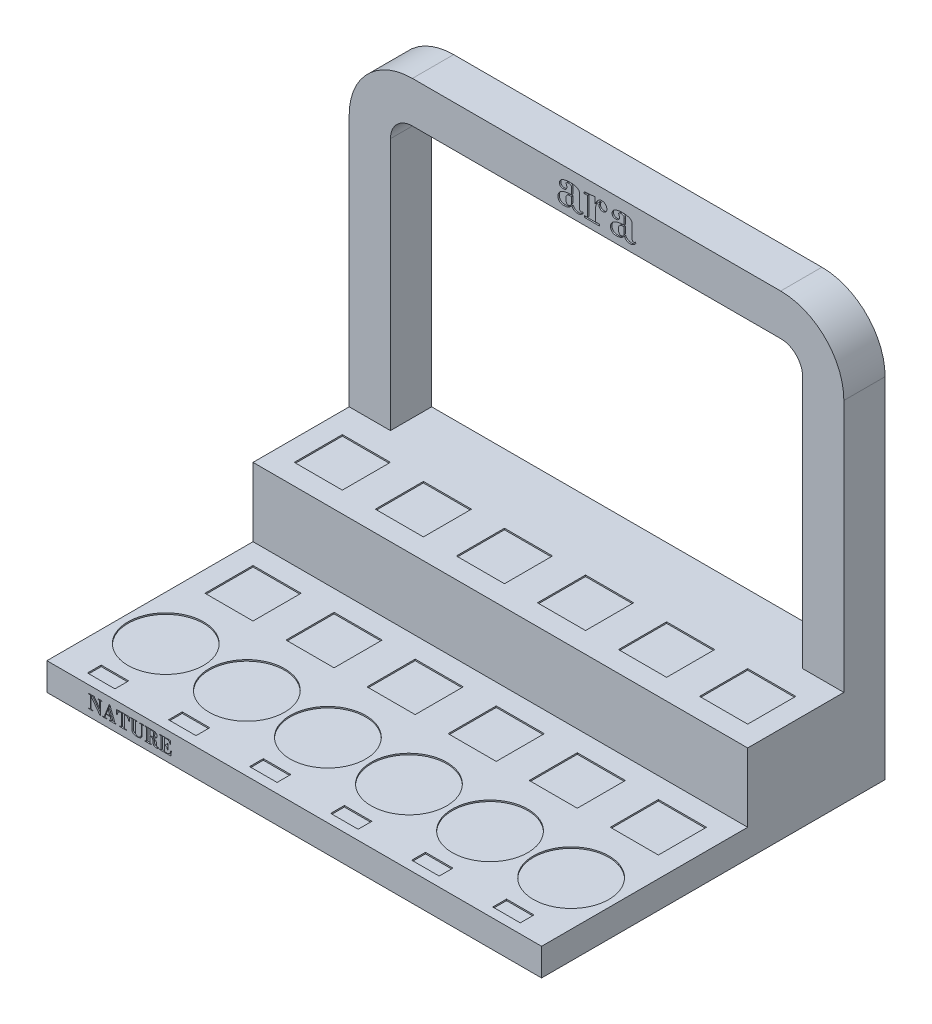
SolidWorks part; units mm, degrees
ref_plane "Front Plane" through (0, 0, 0) normal (0, 0, 1) x (1, 0, 0)
ref_plane "Top Plane" through (0, 0, 0) normal (0, 1, 0) x (1, 0, 0)
ref_plane "Right Plane" through (0, 0, 0) normal (1, 0, 0) x (0, 0, -1)
sketch "Sketch1" plane through (0, 0, 0) normal (1, 0, 0) x (0, 0, -1)
  line L0 (0, 0) -> (150, 0)
  line L1 (150, 0) -> (150, 50)
  line L2 (150, 50) -> (250, 50)
  line L3 (250, 50) -> (250, -20)
  line L4 (250, -20) -> (0, -20)
  line L5 (0, -20) -> (0, 0)
  dimension "D1" = 250
  dimension "D2" = 20
  dimension "D3" = 100
  dimension "D4" = 50
extrude "Boss-Extrude1" add sketch "Sketch1" against normal blind 360
sketch "Sketch4" plane through (0, 0, 0) normal (0, 1, 0) x (1, 0, 0)
  line L0 (-360, 150) -> (0, 150) construction
  line L1 (-345, 135) -> (-310, 135)
  line L2 (-345, 135) -> (-345, 100)
  line L3 (-345, 100) -> (-310, 100)
  line L4 (-310, 135) -> (-310, 100)
  line L6 (-286, 100) -> (-251, 100)
  line L7 (-251, 135) -> (-251, 100)
  line L8 (-286, 135) -> (-251, 135)
  line L9 (-286, 135) -> (-286, 100)
  line L10 (-227, 100) -> (-192, 100)
  line L11 (-192, 135) -> (-192, 100)
  line L12 (-227, 135) -> (-192, 135)
  line L13 (-227, 135) -> (-227, 100)
  line L14 (-168, 100) -> (-133, 100)
  line L15 (-133, 135) -> (-133, 100)
  line L16 (-168, 135) -> (-133, 135)
  line L17 (-168, 135) -> (-168, 100)
  line L18 (-109, 100) -> (-74, 100)
  line L19 (-74, 135) -> (-74, 100)
  line L20 (-109, 135) -> (-74, 135)
  line L21 (-109, 135) -> (-109, 100)
  line L22 (-50, 100) -> (-15, 100)
  line L23 (-15, 135) -> (-15, 100)
  line L24 (-50, 135) -> (-15, 135)
  line L25 (-50, 135) -> (-50, 100)
  line L26 (0, 250) -> (0, 0) construction
  circle A0 centre (-327.5, 54) radius 27.5
  circle A1 centre (-268.5, 54) radius 27.5
  circle A2 centre (-209.5, 54) radius 27.5
  circle A3 centre (-150.5, 54) radius 27.5
  circle A4 centre (-91.5, 54) radius 27.5
  circle A5 centre (-32.5, 54) radius 27.5
  point P30 (-327.5, 100)
  point P42 (-268.5, 100)
  point P44 (-209.5, 100)
  point P46 (-32.5, 100)
  point P47 (-327.5, 81.5)
  dimension "D5" = 55
  dimension "D6" = 15
  dimension "D1" = 35
  dimension "D3" = 15
  dimension "D4" = 6
  dimension "D7" = 24
  dimension "D9" = 46
  dimension "D8" = 6
extrude "Cut-Extrude2" cut sketch "Sketch4" against normal blind 1
sketch "Sketch2" plane through (0, 0, 0) normal (0, 1, 0) x (1, 0, 0)
  line L0 (-327.5, 54) -> (-327.5, 17.0501) construction
  line L5 (-337.5, 17) -> (-317.5, 17)
  line L26 (-337.5, 17) -> (-337.5, 7)
  line L27 (-337.5, 7) -> (-317.5, 7)
  line L28 (-317.5, 17) -> (-317.5, 7)
  line L30 (-360, 0) -> (0, 0) construction
  line L31 (-278.5, 7) -> (-258.5, 7)
  line L32 (-258.5, 17) -> (-258.5, 7)
  line L33 (-278.5, 17) -> (-258.5, 17)
  line L34 (-278.5, 17) -> (-278.5, 7)
  line L35 (-219.5, 7) -> (-199.5, 7)
  line L36 (-199.5, 17) -> (-199.5, 7)
  line L37 (-219.5, 17) -> (-199.5, 17)
  line L38 (-219.5, 17) -> (-219.5, 7)
  line L39 (-160.5, 7) -> (-140.5, 7)
  line L40 (-140.5, 17) -> (-140.5, 7)
  line L41 (-160.5, 17) -> (-140.5, 17)
  line L42 (-160.5, 17) -> (-160.5, 7)
  line L43 (-101.5, 7) -> (-81.5, 7)
  line L44 (-81.5, 17) -> (-81.5, 7)
  line L45 (-101.5, 17) -> (-81.5, 17)
  line L46 (-101.5, 17) -> (-101.5, 7)
  line L47 (-42.5, 7) -> (-22.5, 7)
  line L48 (-22.5, 17) -> (-22.5, 7)
  line L49 (-42.5, 17) -> (-22.5, 17)
  line L50 (-42.5, 17) -> (-42.5, 7)
  line L51 (-268.5, 54) -> (-268.5, -20) construction
  line L52 (-209.5, 26.5) -> (-209.5, -5.4255) construction
  line L53 (-150.5, 26.5) -> (-150.5, 2.6241) construction
  line L54 (-91.5, 26.5) -> (-91.5, -3.008) construction
  line L55 (-32.5, 26.5) -> (-32.5, -8.6779) construction
  circle A1 centre (-209.5, 54) radius 27.5 construction
  circle A4 centre (-209.5, 54) radius 27.5 construction
  circle A5 centre (-150.5, 54) radius 27.5 construction
  circle A6 centre (-91.5, 54) radius 27.5 construction
  circle A7 centre (-32.5, 54) radius 27.5 construction
  circle A8 centre (-32.5, 54) radius 27.5 construction
  point P8 (-327.5, 17)
  point P31 (-268.5, 17)
  dimension "D1" = 20
  dimension "D2" = 10
  dimension "D3" = 7
  dimension "D4" = 6
extrude "Cut-Extrude3" cut sketch "Sketch2" against normal blind 1
sketch "Sketch5" plane through (0, 50, 0) normal (0, 1, 0) x (1, 0, 0)
  line L0 (-360, 250) -> (0, 250) construction
  line L2 (-345, 200) -> (-310, 200)
  line L3 (-345, 200) -> (-345, 165)
  line L4 (-345, 165) -> (-310, 165)
  line L5 (-310, 200) -> (-310, 165)
  line L7 (-360, 250) -> (-360, 150) construction
  line L8 (-286, 200) -> (-251, 200)
  line L9 (-286, 200) -> (-286, 165)
  line L10 (-286, 165) -> (-251, 165)
  line L11 (-251, 200) -> (-251, 165)
  line L12 (-227, 200) -> (-192, 200)
  line L13 (-227, 200) -> (-227, 165)
  line L14 (-227, 165) -> (-192, 165)
  line L15 (-192, 200) -> (-192, 165)
  line L16 (-168, 200) -> (-133, 200)
  line L17 (-168, 200) -> (-168, 165)
  line L18 (-168, 165) -> (-133, 165)
  line L19 (-133, 200) -> (-133, 165)
  line L20 (-109, 200) -> (-74, 200)
  line L21 (-109, 200) -> (-109, 165)
  line L22 (-109, 165) -> (-74, 165)
  line L23 (-74, 200) -> (-74, 165)
  line L24 (-50, 200) -> (-15, 200)
  line L25 (-50, 200) -> (-50, 165)
  line L26 (-50, 165) -> (-15, 165)
  line L27 (-15, 200) -> (-15, 165)
  line L28 (0, 250) -> (0, 0) construction
  dimension "D1" = 35
  dimension "D3" = 50
  dimension "D4" = 15
  dimension "D6" = 15
  dimension "D5" = 6
extrude "Cut-Extrude4" cut sketch "Sketch5" against normal blind 1
sketch "Sketch6" plane through (0, 0, -250) normal (0, 0, -1) x (-1, 0, 0)
  line L0 (0, 50) -> (0, 234)
  line L1 (46, 280) -> (314, 280)
  line L3 (360, 50) -> (0, 50)
  line L5 (360, -20) -> (0, -20) construction
  line L6 (180, 50) -> (180, 341.2039) construction
  line L7 (360, 50) -> (360, 234)
  line L8 (46, 250) -> (314, 250)
  line L9 (330, 80) -> (330, 234)
  line L10 (330, 80) -> (30, 80)
  line L11 (30, 80) -> (30, 234)
  line L12 (0, -20) -> (0, 50) construction
  arc A0 (0, 234) -> (46, 280) centre (46, 234) cw
  arc A2 (360, 234) -> (314, 280) centre (314, 234) ccw
  arc A3 (30, 234) -> (46, 250) centre (46, 234) cw
  arc A4 (330, 234) -> (314, 250) centre (314, 234) ccw
  point P12 (180, 280)
  dimension "D3" = 16
  dimension "D4" = 46
  dimension "D1" = 300
  dimension "D2" = 30
  dimension "D5" = 134
extrude "Boss-Extrude2" add sketch "Sketch6" against normal blind 30 contours L7 A2 L1 A0 L0 L3
sketch "Sketch7" plane through (0, 0, -220) normal (0, 0, 1) x (1, 0, 0)
  line L1 (-330, 50) -> (-30, 50)
  line L4 (0, 50) -> (0, 234)
  line L5 (-46, 280) -> (-314, 280)
  line L6 (-360, 234) -> (-360, 50)
  line L7 (-360, 50) -> (0, 50)
  line L8 (0, 50) -> (0, 234)
  line L9 (-46, 280) -> (-314, 280)
  line L10 (-360, 234) -> (-360, 50)
  line L11 (-360, 50) -> (0, 50)
  line L12 (-46, 250) -> (-314, 250)
  line L13 (-330, 234) -> (-330, 80)
  line L14 (-330, 80) -> (-30, 80)
  line L15 (-30, 80) -> (-30, 234)
  line L16 (-46, 250) -> (-314, 250)
  line L17 (-330, 234) -> (-330, 50)
  line L19 (-30, 50) -> (-30, 234)
  arc A2 (0, 234) -> (-46, 280) centre (-46, 234) ccw
  arc A3 (-314, 280) -> (-360, 234) centre (-314, 234) ccw
  arc A4 (0, 234) -> (-46, 280) centre (-46, 234) ccw
  arc A5 (-314, 280) -> (-360, 234) centre (-314, 234) ccw
  arc A6 (-314, 250) -> (-330, 234) centre (-314, 234) ccw
  arc A7 (-30, 234) -> (-46, 250) centre (-46, 234) ccw
  arc A8 (-314, 250) -> (-330, 234) centre (-314, 234) ccw
  arc A9 (-30, 234) -> (-46, 250) centre (-46, 234) ccw
  line M13 (-360, 50) -> (0, 50)
  dimension "D1" = 0
  dimension "D2" = 0
extrude "Cut-Extrude9" cut sketch "Sketch7" against normal through all contours L19 A9 L16 A8 L17 M13
sketch "Sketch9" plane through (0, 0, 0) normal (0, 0, 1) x (1, 0, 0)
  line L1 (-360, 0) -> (-360, -20) construction
  line L2 (-360, -20) -> (0, -20) construction
  text T0 "NATURE" font "Bodoni Bd BT" height in points 36
  dimension "D1" = 30
  dimension "D2" = 5
extrude "Cut-Extrude10" cut sketch "Sketch9" against normal blind 1
sketch "Sketch10" plane through (0, 0, -220) normal (0, 0, 1) x (1, 0, 0)
  line L0 (-46, 250) -> (-314, 250) construction
  line L1 (-360, 50) -> (-360, 234) construction
  text T0 "ara" font "Bodoni Bd BT" height in points 100
  dimension "D1" = 5
  dimension "D2" = 150
extrude "Cut-Extrude11" cut sketch "Sketch10" against normal blind 1
sketch "Sketch11" plane through (0, 0, -250) normal (0, 0, -1) x (-1, 0, 0)
  circle A0 centre (326.177, 0) radius 11.9288
  point P2 (326.177, 0)
  point P4 (323.0266, -20)
extrude "Cut-Extrude14" cut sketch "Sketch11" against normal blind 10
